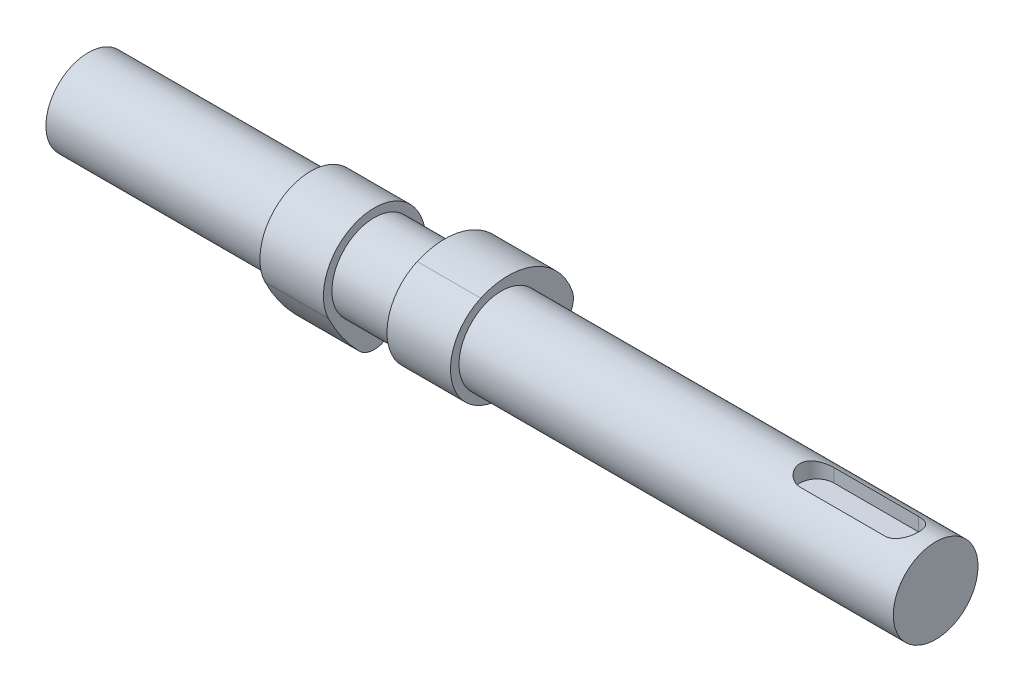
SolidWorks part; units mm, degrees
ref_plane "Front Plane" through (0, 0, 0) normal (0, 0, 1) x (1, 0, 0)
ref_plane "Top Plane" through (0, 0, 0) normal (0, 1, 0) x (1, 0, 0)
ref_plane "Right Plane" through (0, 0, 0) normal (1, 0, 0) x (0, 0, -1)
sketch "Sketch1" plane through (0, 0, 0) normal (1, 0, 0) x (0, 0, -1)
  circle A0 centre (0, 0) radius 10
  dimension "D1" = 20
extrude "Boss-Extrude1" add sketch "Sketch1" against normal blind 75 and the other way blind 125
sketch "Sketch2" plane through (0, 0, 0) normal (1, 0, 0) x (0, 0, -1)
  arc A6 (15.4795, -3.5877) -> (16.7127, 1.6619) centre (11.997, 0) ccw
  circle A7 centre (0, 0) radius 12
  arc A8 (-4.8671, 10.9687) -> (5.3062, -10.7631) centre (0, 0) ccw
  arc A9 (-4.8671, 10.9687) -> (16.7127, 1.6619) centre (1.6224, -3.6562) cw
  arc A10 (5.3062, -10.7631) -> (15.4795, -3.5877) centre (-12.3812, 25.1139) ccw
  point P0 (3.9943, -11.3157)
  dimension "D1" = 2
  dimension "D2" = 10
  dimension "D3" = 16
  dimension "D4" = 40
  dimension "D5" = 12.5
extrude "Boss-Extrude2" add sketch "Sketch2" along normal mid plane 15 from offset 15 separate body
mirror "Mirror4" about plane through (0, 0, 0) normal (1, 0, 0) of bodies 102
move or copy body "Body-Move/Copy1" bodies to move or copy 103 copy no rotation origin (0, 0, 0) rotation axis (-1, 0, 0) rotation angle 90
ref_plane "Plane1" through (0, 10, 0) normal (0, 1, 0) x (1, 0, 0)
sketch "Sketch4" plane through (0, 10, 0) normal (0, 1, 0) x (1, 0, 0)
  line L0 (125, 0) -> (59.1513, 0) construction
  line L1 (125, -10) -> (125, 10) construction
  line L2 (117, 0) -> (97, 0) construction
  line L3 (117, -4) -> (97, -4)
  line L4 (117, 4) -> (97, 4)
  arc A0 (117, -4) -> (117, 4) centre (117, 0) ccw
  arc A1 (97, 4) -> (97, -4) centre (97, 0) ccw
  point P7 (107, 0)
  dimension "D3" = 4
  dimension "D1" = 20
  dimension "D2" = 8
extrude "Cut-Extrude1" cut sketch "Sketch4" against normal blind 4
